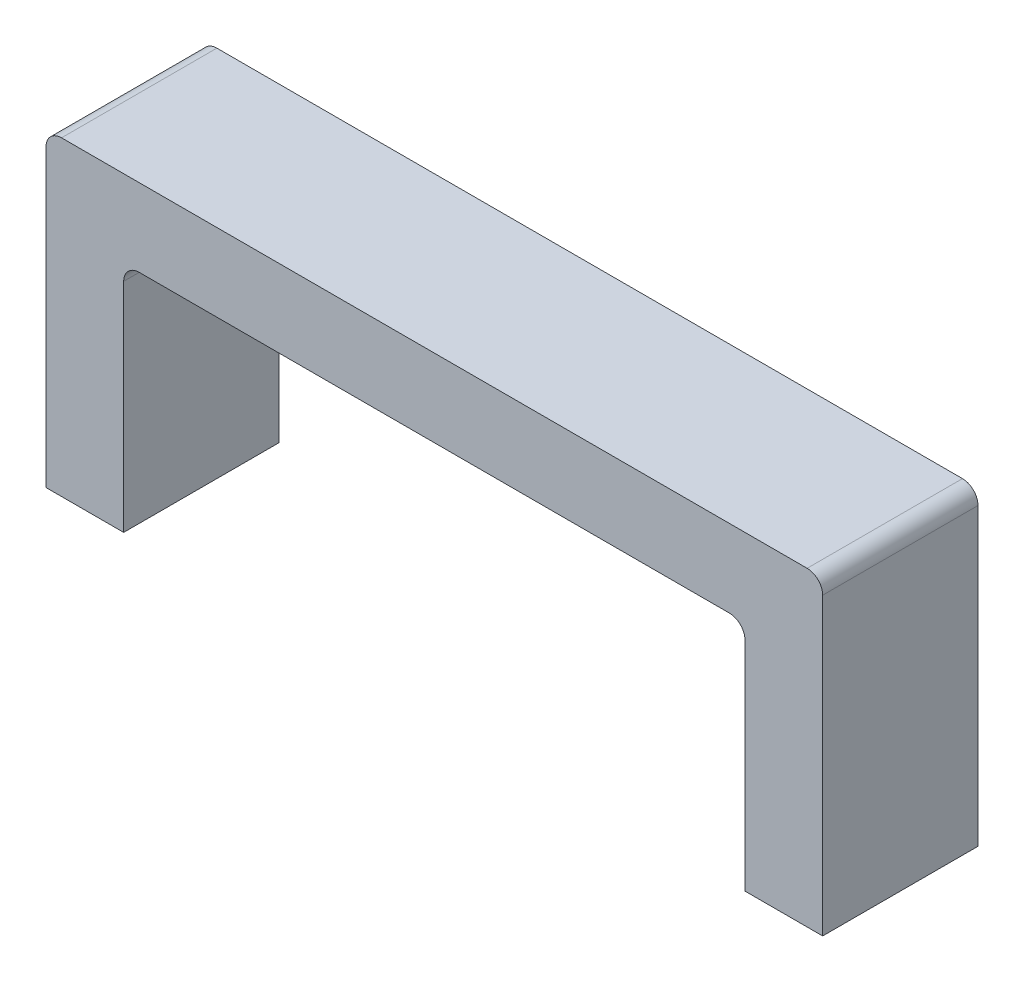
SolidWorks part; units mm, degrees
material "Acrylic (Medium-high impact)"
ref_plane "Front Plane" through (0, 0, 0) normal (0, 0, 1) x (1, 0, 0)
ref_plane "Top Plane" through (0, 0, 0) normal (0, 1, 0) x (1, 0, 0)
ref_plane "Right Plane" through (0, 0, 0) normal (1, 0, 0) x (0, 0, -1)
sketch "Sketch1" plane through (0, 0, 0) normal (0, 0, 1) x (1, 0, 0)
  line L0 (0, 0) -> (0, 48.26)
  line L1 (2.54, 50.8) -> (124.46, 50.8)
  line L2 (127, 48.26) -> (127, 0)
  line L3 (0, 0) -> (12.7, 0)
  line L4 (12.7, 0) -> (12.7, 35.56)
  line L5 (15.24, 38.1) -> (111.76, 38.1)
  line L6 (114.3, 35.56) -> (114.3, 0)
  line L7 (114.3, 0) -> (127, 0)
  arc A0 (15.24, 38.1) -> (12.7, 35.56) centre (15.24, 35.56) ccw
  arc A1 (114.3, 35.56) -> (111.76, 38.1) centre (111.76, 35.56) ccw
  arc A2 (124.46, 50.8) -> (127, 48.26) centre (124.46, 48.26) cw
  arc A3 (2.54, 50.8) -> (0, 48.26) centre (2.54, 48.26) ccw
  point P15 (127, 50.8)
  point P18 (0, 50.8)
  point P19 (0, 24.13)
  dimension "D3" = 2.54
  dimension "D4" = 2.54
  dimension "D5" = 2.54
  dimension "D1" = 50.8
  dimension "D2" = 127
  dimension "D6" = 12.7
  dimension "D7" = 12.7
  dimension "D8" = 12.7
extrude "Boss-Extrude1" add sketch "Sketch1" along normal blind 25.4
